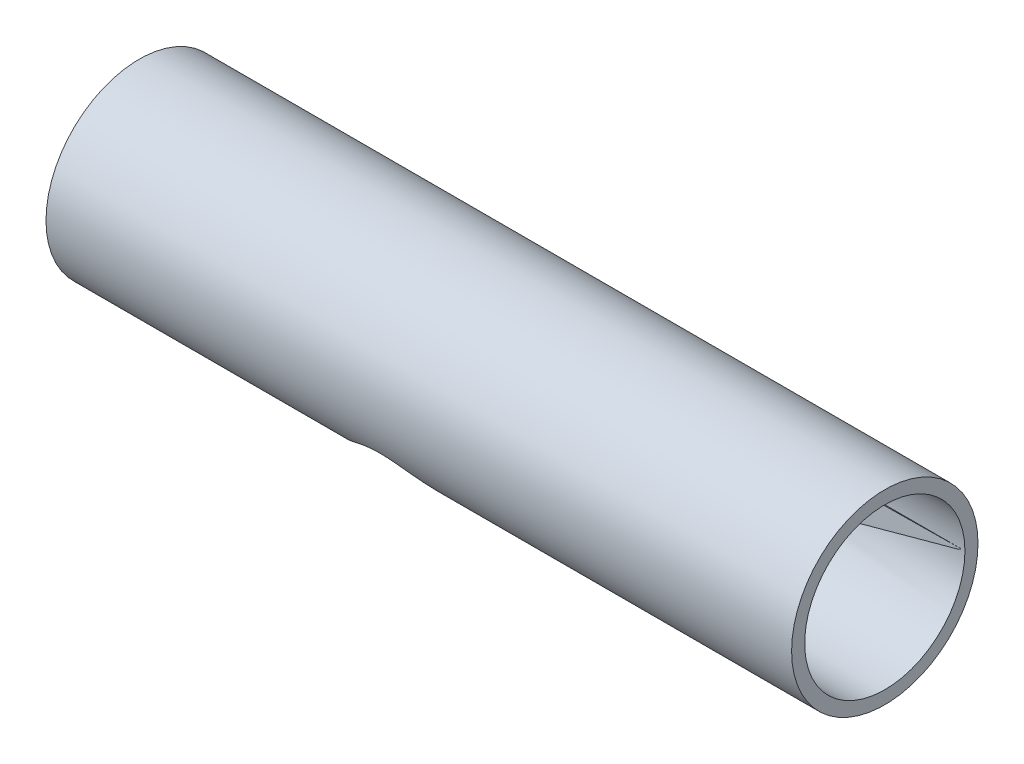
SolidWorks part; units mm, degrees
ref_plane "Front" through (0, 0, 0) normal (0, 0, 1) x (1, 0, 0)
ref_plane "Top" through (0, 0, 0) normal (0, 1, 0) x (1, 0, 0)
ref_plane "Right" through (0, 0, 0) normal (1, 0, 0) x (0, 0, -1)
sketch "Sketch1" plane through (0, 0, 0) normal (1, 0, 0) x (0, 0, -1)
  circle A0 centre (0, 0) radius 25
  dimension "D1" = 50
extrude "Boss-Extrude3" add sketch "Sketch1" along normal blind 200
sketch "Sketch3" plane through (200, 0, 0) normal (1, 0, 0) x (0, 0, -1)
  circle A0 centre (0, 0) radius 21.5
  dimension "D1" = 43
extrude "Cut-Extrude1" cut sketch "Sketch3" against normal blind 190
sketch "Sketch5" plane through (0, 0, 0) normal (-1, 0, 0) x (0, 0, 1)
  circle A0 centre (0, 0) radius 10
  dimension "D1" = 20
extrude "Cut-Extrude2" cut sketch "Sketch5" against normal up to next
sketch "Sketch6" plane through (0, 0, 0) normal (0, 1, 0) x (1, 0, 0)
  line L0 (0, 25) -> (0, -25) construction
  circle A0 centre (86, 0) radius 21.5
  dimension "D1" = 43
  dimension "D2" = 86
extrude "Cut-Extrude3" cut sketch "Sketch6" against normal up to next
